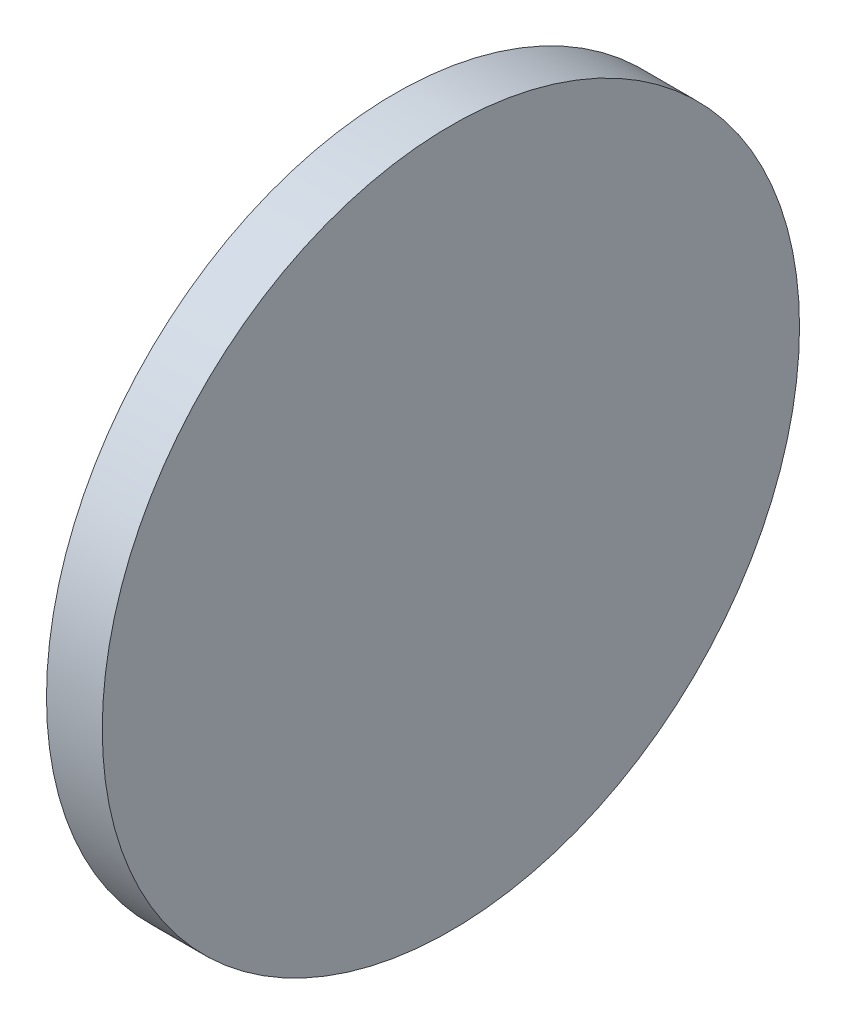
SolidWorks part; units mm, degrees
ref_plane "前视基准面" through (0, 0, 0) normal (0, 0, 1) x (1, 0, 0)
ref_plane "上视基准面" through (0, 0, 0) normal (0, 1, 0) x (1, 0, 0)
ref_plane "右视基准面" through (0, 0, 0) normal (1, 0, 0) x (0, 0, -1)
sketch "草图1" plane through (0, 0, 0) normal (0, 0, 1) x (1, 0, 0)
  line L0 (500.7376, 154.5864) -> (543.0834, 154.5864) construction
  line L1 (520.3697, 154.5864) -> (520.3697, 179.5864)
  line L2 (520.3697, 179.5864) -> (524.3697, 179.5864)
  line L3 (524.3697, 179.5864) -> (524.3697, 154.5864)
  line L4 (524.3697, 154.5864) -> (520.3697, 154.5864)
revolve "旋转1" add sketch "草图1" angle 360 about L0
